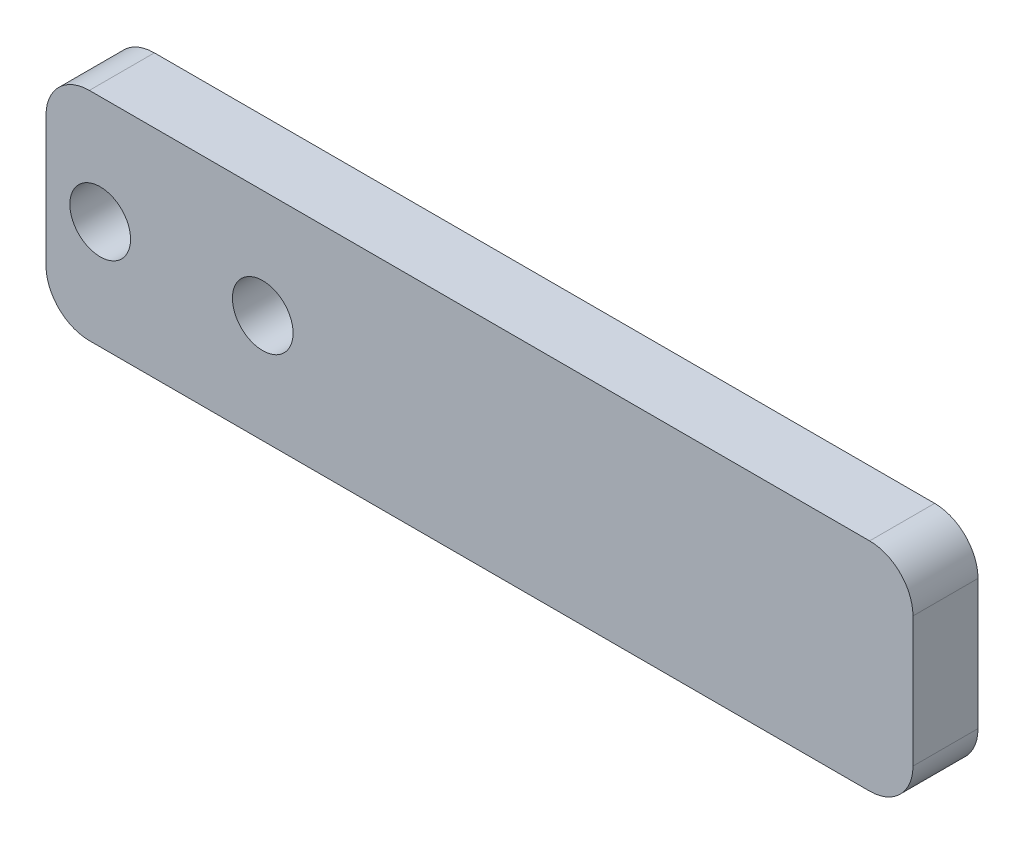
SolidWorks part; units mm, degrees
ref_plane "Plan de face" through (0, 0, 0) normal (0, 0, 1) x (1, 0, 0)
ref_plane "Plan de dessus" through (0, 0, 0) normal (0, 1, 0) x (1, 0, 0)
ref_plane "Plan de droite" through (0, 0, 0) normal (1, 0, 0) x (0, 0, -1)
sketch "Esquisse1" plane through (0, 0, 0) normal (0, 0, 1) x (1, 0, 0)
  line L1 (-20, -5) -> (20, -5)
  line L2 (-20, -5) -> (-20, 5)
  line L3 (-20, 5) -> (20, 5)
  line L4 (20, -5) -> (20, 5)
  line L5 (-20, -5) -> (20, 5) construction
  line L6 (-20, 5) -> (20, -5) construction
  circle A0 centre (-10, 0) radius 1.4
  circle A1 centre (-17.5, 0) radius 1.4
  point P0 (0, 0)
  dimension "D4" = 2.8
  dimension "D1" = 40
  dimension "D2" = 10
  dimension "D3" = 10
  dimension "D5" = 2.5
  dimension "D6" = 5
extrude "Boss.-Extru.1" add sketch "Esquisse1" along normal blind 3
fillet "Congé1" radius 2 4 edges at (-20, -5, 1.5) (-20, 5, 1.5) (20, -5, 1.5) (20, 5, 1.5)
